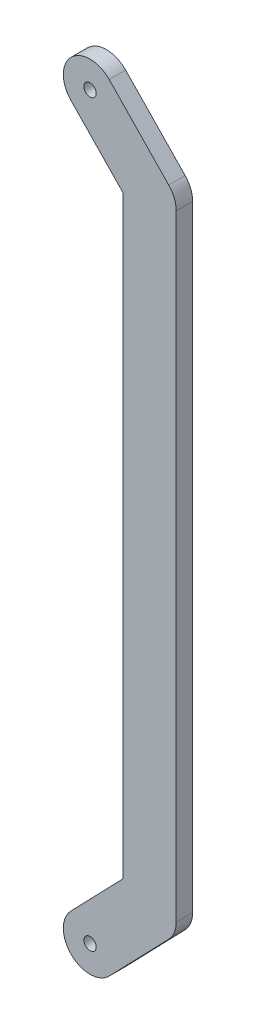
SolidWorks part; units mm, degrees
ref_plane "前视基准面" through (0, 0, 0) normal (0, 0, 1) x (1, 0, 0)
ref_plane "上视基准面" through (0, 0, 0) normal (0, 1, 0) x (1, 0, 0)
ref_plane "右视基准面" through (0, 0, 0) normal (1, 0, 0) x (0, 0, -1)
other "Configuration Table"
sketch "草图1" plane through (0, 0, 0) normal (0, 0, 1) x (1, 0, 0)
  line L0 (0, 0) -> (14.4853, 15) construction
  line L1 (-4.6757, 4.5153) -> (9.8096, 19.5153)
  line L2 (4.6757, -4.5153) -> (19.161, 10.4847)
  line L3 (14.4853, 15) -> (14.4853, 165) construction
  line L4 (7.9853, 15) -> (7.9853, 165)
  line L5 (20.9853, 15) -> (20.9853, 165)
  line L6 (14.4853, 165) -> (0, 180) construction
  line L7 (9.8096, 160.4847) -> (-4.6757, 175.4847)
  line L8 (19.161, 169.5153) -> (4.6757, 184.5153)
  line L9 (0, 180) -> (0, 0) construction
  arc A0 (-4.6757, 4.5153) -> (4.6757, -4.5153) centre (0, 0) ccw
  arc A1 (19.161, 10.4847) -> (9.8096, 19.5153) centre (14.4853, 15) ccw
  arc A2 (7.9853, 15) -> (20.9853, 15) centre (14.4853, 15) ccw
  arc A3 (20.9853, 165) -> (7.9853, 165) centre (14.4853, 165) ccw
  arc A4 (9.8096, 160.4847) -> (19.161, 169.5153) centre (14.4853, 165) ccw
  arc A5 (4.6757, 184.5153) -> (-4.6757, 175.4847) centre (0, 180) ccw
  point P3 (7.2427, 7.5)
  point P8 (14.4853, 90)
  point P15 (7.2427, 172.5)
  dimension "D3" = 6.5
  dimension "D1" = 136
  dimension "D2" = 136
  dimension "D4" = 180
  dimension "D5" = 150
extrude "凸台-拉伸1" add sketch "草图1" along normal blind 4 contours A4 L7 L4 L1 A1 L5 | L8 A5 L7 L4 A3 | L7 A4 A3 L4 | L4 A2 A1 L1 | A2 L4 L1 A0 L2
sketch "草图2" plane through (0, 0, 4) normal (0, 0, 1) x (1, 0, 0)
  point P0 (0, 0)
  point P3 (0, 180)
hole_wizard "M3 螺纹孔1" positions "草图2" profile "草图3" tap size "M3" standard "GB"
sketch "草图3" plane through (0, 0, 4) normal (1, 0, 0) x (0, -1, 0)
  line L0 (0, 0) -> (0, 10.9013)
  line L1 (0, 10.9013) -> (1.5, 10)
  line L2 (1.5, 10) -> (1.5, 0)
  line L5 (1.5, 0) -> (0, 0)
  line L10 (0, 10.9013) -> (-1.5, 10) construction
  line L11 (0, -6.35) -> (0, 107.95) construction
  dimension "螺纹孔钻头直径" = 3
  dimension "螺纹孔钻头深度" = 10
  dimension "导头角度" = 118
cosmetic thread "孔螺蚊线1" parameters "D1"=6, "D2"=3
cosmetic thread "孔螺蚊线2" parameters "D1"=6, "D2"=3
